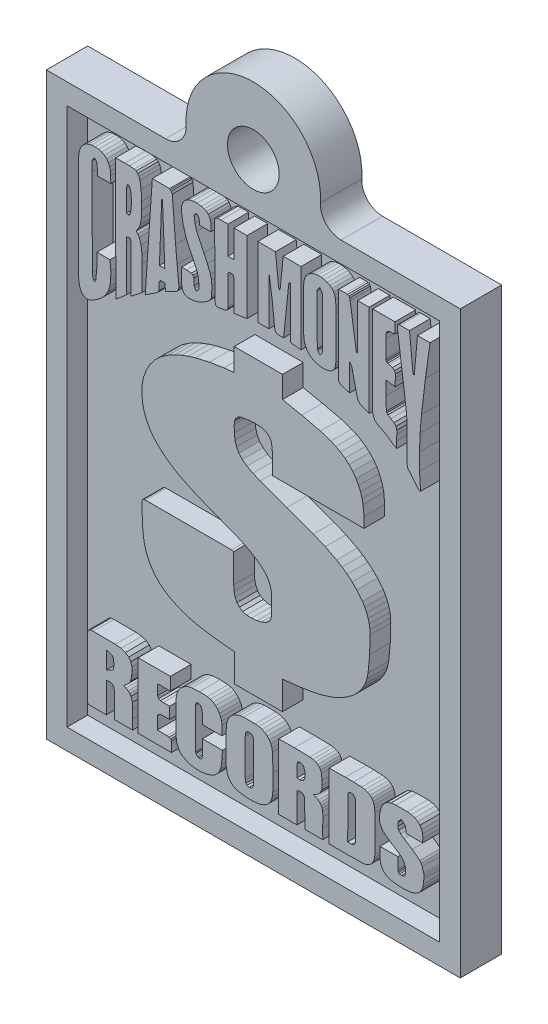
SolidWorks part; units mm, degrees
ref_plane "Front Plane" through (0, 0, 0) normal (0, 0, 1) x (1, 0, 0)
ref_plane "Top Plane" through (0, 0, 0) normal (0, 1, 0) x (1, 0, 0)
ref_plane "Right Plane" through (0, 0, 0) normal (1, 0, 0) x (0, 0, -1)
sketch "Sketch3" plane through (0, 0, 0) normal (0, 0, 1) x (1, 0, 0)
  line L1 (0, 0) -> (63.5, 0)
  line L2 (0, 0) -> (0, 88.9)
  line L3 (0, 88.9) -> (63.5, 88.9)
  line L4 (63.5, 0) -> (63.5, 88.9)
  dimension "D1" = 63.5
  dimension "D2" = 88.9
extrude "Boss-Extrude1" add sketch "Sketch3" along normal blind 6.35
sketch "Sketch4" plane through (0, 0, 6.35) normal (0, 0, 1) x (1, 0, 0)
  line L0 (3.175, 85.725) -> (3.175, 3.175)
  line L1 (3.175, 3.175) -> (60.325, 3.175)
  line L2 (60.325, 3.175) -> (60.325, 85.725)
  line L3 (60.325, 85.725) -> (3.175, 85.725)
  line L4 (0, 88.9) -> (0, 0)
  line L5 (0, 0) -> (63.5, 0)
  line L6 (63.5, 0) -> (63.5, 88.9)
  line L7 (63.5, 88.9) -> (0, 88.9)
  line L8 (0, 88.9) -> (0, 0) construction
  line L9 (0, 0) -> (63.5, 0) construction
  line L10 (63.5, 0) -> (63.5, 88.9) construction
  line L11 (63.5, 88.9) -> (0, 88.9) construction
  dimension "D1" = 0
  dimension "D2" = 3.175
extrude "Cut-Extrude1" cut sketch "Sketch4" against normal blind 3.175
sketch "Sketch5" plane through (0, 0, 3.175) normal (0, 0, 1) x (1, 0, 0)
  line L0 (36.2423, 26.0782) -> (36.2187, 21.7427)
  line L1 (38.9004, 26.3618) -> (36.2423, 26.0782)
  line L2 (40.6115, 26.6257) -> (38.9004, 26.3618)
  line L3 (42.2938, 26.9938) -> (40.6115, 26.6257)
  line L4 (43.9274, 27.5213) -> (42.2938, 26.9938)
  line L5 (44.7197, 27.8622) -> (43.9274, 27.5213)
  line L6 (45.4924, 28.2637) -> (44.7197, 27.8622)
  line L7 (46.2282, 28.7206) -> (45.4924, 28.2637)
  line L8 (46.9067, 29.2251) -> (46.2282, 28.7206)
  line L9 (47.5204, 29.7805) -> (46.9067, 29.2251)
  line L10 (48.0618, 30.3902) -> (47.5204, 29.7805)
  line L11 (48.5235, 31.0575) -> (48.0618, 30.3902)
  line L12 (48.898, 31.7857) -> (48.5235, 31.0575)
  line L13 (49.1778, 32.5781) -> (48.898, 31.7857)
  line L14 (49.3554, 33.4381) -> (49.1778, 32.5781)
  line L15 (49.5932, 36.04) -> (49.3554, 33.4381)
  line L16 (49.6626, 38.6597) -> (49.5932, 36.04)
  line L17 (49.6353, 39.3647) -> (49.6626, 38.6597)
  line L18 (49.5376, 40.0448) -> (49.6353, 39.3647)
  line L19 (49.3721, 40.7006) -> (49.5376, 40.0448)
  line L20 (49.1413, 41.3325) -> (49.3721, 40.7006)
  line L21 (48.848, 41.9412) -> (49.1413, 41.3325)
  line L22 (48.4947, 42.5272) -> (48.848, 41.9412)
  line L23 (47.6188, 43.6332) -> (48.4947, 42.5272)
  line L24 (46.9047, 44.3394) -> (47.6188, 43.6332)
  line L25 (46.1477, 44.9744) -> (46.9047, 44.3394)
  line L26 (45.3524, 45.5458) -> (46.1477, 44.9744)
  line L27 (44.5237, 46.0609) -> (45.3524, 45.5458)
  line L28 (42.7845, 46.9525) -> (44.5237, 46.0609)
  line L29 (40.9678, 47.7089) -> (42.7845, 46.9525)
  line L30 (36.8862, 49.193) -> (40.9678, 47.7089)
  line L31 (32.8046, 50.6859) -> (36.8862, 49.193)
  line L32 (31.6833, 51.1579) -> (32.8046, 50.6859)
  line L33 (30.7787, 51.6416) -> (31.6833, 51.1579)
  line L34 (30.0715, 52.161) -> (30.7787, 51.6416)
  line L35 (29.5425, 52.74) -> (30.0715, 52.161)
  line L36 (29.1725, 53.4027) -> (29.5425, 52.74)
  line L37 (28.9421, 54.173) -> (29.1725, 53.4027)
  line L38 (28.8321, 55.0748) -> (28.9421, 54.173)
  line L39 (28.8234, 56.2029) -> (28.8321, 55.0748)
  line L40 (28.8935, 56.7347) -> (28.8234, 56.2029)
  line L41 (29.101, 57.179) -> (28.8935, 56.7347)
  line L42 (29.4414, 57.5103) -> (29.101, 57.179)
  line L43 (29.9102, 57.7032) -> (29.4414, 57.5103)
  line L44 (31.2939, 57.9262) -> (29.9102, 57.7032)
  line L45 (31.9952, 57.964) -> (31.2939, 57.9262)
  line L46 (32.6864, 57.9277) -> (31.9952, 57.964)
  line L47 (33.1952, 57.8398) -> (32.6864, 57.9277)
  line L48 (33.6177, 57.6986) -> (33.1952, 57.8398)
  line L49 (33.9596, 57.5018) -> (33.6177, 57.6986)
  line L50 (34.2266, 57.2469) -> (33.9596, 57.5018)
  line L51 (34.4245, 56.9317) -> (34.2266, 57.2469)
  line L52 (34.5587, 56.5538) -> (34.4245, 56.9317)
  line L53 (34.6593, 55.6004) -> (34.5587, 56.5538)
  line L54 (34.6593, 52.3398) -> (34.6593, 55.6004)
  line L55 (48.7175, 52.3398) -> (34.6593, 52.3398)
  line L56 (48.7369, 53.9223) -> (48.7175, 52.3398)
  line L57 (48.589, 55.4572) -> (48.7369, 53.9223)
  line L58 (48.4306, 56.2043) -> (48.589, 55.4572)
  line L59 (48.2042, 56.9366) -> (48.4306, 56.2043)
  line L60 (47.9011, 57.6532) -> (48.2042, 56.9366)
  line L61 (47.5125, 58.353) -> (47.9011, 57.6532)
  line L62 (47.0008, 59.066) -> (47.5125, 58.353)
  line L63 (46.427, 59.6866) -> (47.0008, 59.066)
  line L64 (45.7974, 60.2234) -> (46.427, 59.6866)
  line L65 (45.1188, 60.6847) -> (45.7974, 60.2234)
  line L66 (44.3975, 61.079) -> (45.1188, 60.6847)
  line L67 (43.64, 61.4147) -> (44.3975, 61.079)
  line L68 (42.0428, 61.9443) -> (43.64, 61.4147)
  line L69 (39.1854, 62.6133) -> (42.0428, 61.9443)
  line L70 (36.2305, 63.2202) -> (39.1854, 62.6133)
  line L71 (36.2305, 66.5634) -> (36.2305, 63.2202)
  line L72 (28.8234, 66.5634) -> (36.2305, 66.5634)
  line L73 (28.8234, 63.102) -> (28.8234, 66.5634)
  line L74 (27.2286, 62.9248) -> (28.8234, 63.102)
  line L75 (25.0104, 62.569) -> (27.2286, 62.9248)
  line L76 (22.8354, 62.0713) -> (25.0104, 62.569)
  line L77 (21.7707, 61.7458) -> (22.8354, 62.0713)
  line L78 (20.7246, 61.3566) -> (21.7707, 61.7458)
  line L79 (19.6999, 60.8943) -> (20.7246, 61.3566)
  line L80 (18.6991, 60.3495) -> (19.6999, 60.8943)
  line L81 (17.6197, 59.6008) -> (18.6991, 60.3495)
  line L82 (16.6977, 58.7373) -> (17.6197, 59.6008)
  line L83 (15.9387, 57.7724) -> (16.6977, 58.7373)
  line L84 (15.3485, 56.7197) -> (15.9387, 57.7724)
  line L85 (14.9327, 55.5929) -> (15.3485, 56.7197)
  line L86 (14.6971, 54.4054) -> (14.9327, 55.5929)
  line L87 (14.6472, 53.1708) -> (14.6971, 54.4054)
  line L88 (14.7888, 51.9027) -> (14.6472, 53.1708)
  line L89 (15.0103, 50.9982) -> (14.7888, 51.9027)
  line L90 (15.3245, 50.1597) -> (15.0103, 50.9982)
  line L91 (15.7246, 49.3824) -> (15.3245, 50.1597)
  line L92 (16.2035, 48.6614) -> (15.7246, 49.3824)
  line L93 (16.7545, 47.9919) -> (16.2035, 48.6614)
  line L94 (17.3705, 47.3691) -> (16.7545, 47.9919)
  line L95 (18.0446, 46.7881) -> (17.3705, 47.3691)
  line L96 (18.77, 46.244) -> (18.0446, 46.7881)
  line L97 (19.6487, 45.6648) -> (18.77, 46.244)
  line L98 (20.5541, 45.1435) -> (19.6487, 45.6648)
  line L99 (22.4278, 44.2357) -> (20.5541, 45.1435)
  line L100 (24.357, 43.4431) -> (22.4278, 44.2357)
  line L101 (26.3071, 42.6881) -> (24.357, 43.4431)
  line L102 (29.4274, 41.4713) -> (26.3071, 42.6881)
  line L103 (30.9405, 40.7644) -> (29.4274, 41.4713)
  line L104 (32.3793, 39.9001) -> (30.9405, 40.7644)
  line L105 (33.3403, 39.0999) -> (32.3793, 39.9001)
  line L106 (33.7337, 38.6523) -> (33.3403, 39.0999)
  line L107 (34.0598, 38.1679) -> (33.7337, 38.6523)
  line L108 (34.3117, 37.6432) -> (34.0598, 38.1679)
  line L109 (34.4825, 37.0743) -> (34.3117, 37.6432)
  line L110 (34.5652, 36.4574) -> (34.4825, 37.0743)
  line L111 (34.553, 35.789) -> (34.5652, 36.4574)
  line L112 (34.5205, 34.7848) -> (34.553, 35.789)
  line L113 (34.5412, 33.7807) -> (34.5205, 34.7848)
  line L114 (34.4919, 33.2889) -> (34.5412, 33.7807)
  line L115 (34.3153, 32.8769) -> (34.4919, 33.2889)
  line L116 (34.0212, 32.5447) -> (34.3153, 32.8769)
  line L117 (33.6197, 32.2921) -> (34.0212, 32.5447)
  line L118 (32.9877, 32.047) -> (33.6197, 32.2921)
  line L119 (32.3202, 31.8905) -> (32.9877, 32.047)
  line L120 (31.4677, 31.7998) -> (32.3202, 31.8905)
  line L121 (30.7343, 31.8386) -> (31.4677, 31.7998)
  line L122 (30.1182, 32.0078) -> (30.7343, 31.8386)
  line L123 (29.6179, 32.3084) -> (30.1182, 32.0078)
  line L124 (29.2316, 32.7413) -> (29.6179, 32.3084)
  line L125 (28.9578, 33.3076) -> (29.2316, 32.7413)
  line L126 (28.7947, 34.0081) -> (28.9578, 33.3076)
  line L127 (28.7407, 34.8439) -> (28.7947, 34.0081)
  line L128 (28.7407, 39.2622) -> (28.7407, 34.8439)
  line L129 (28.4099, 39.3331) -> (28.7407, 39.2622)
  line L130 (15.2141, 39.3449) -> (28.4099, 39.3331)
  line L131 (14.9446, 39.3091) -> (15.2141, 39.3449)
  line L132 (14.7682, 39.2002) -> (14.9446, 39.3091)
  line L133 (14.6759, 39.0159) -> (14.7682, 39.2002)
  line L134 (14.6589, 38.7542) -> (14.6759, 39.0159)
  line L135 (14.7313, 36.4417) -> (14.6589, 38.7542)
  line L136 (14.7935, 35.2887) -> (14.7313, 36.4417)
  line L137 (14.9188, 34.1469) -> (14.7935, 35.2887)
  line L138 (15.1022, 33.2367) -> (14.9188, 34.1469)
  line L139 (15.3694, 32.377) -> (15.1022, 33.2367)
  line L140 (15.721, 31.5694) -> (15.3694, 32.377)
  line L141 (16.1577, 30.8154) -> (15.721, 31.5694)
  line L142 (16.6803, 30.1168) -> (16.1577, 30.8154)
  line L143 (17.2895, 29.4753) -> (16.6803, 30.1168)
  line L144 (17.9858, 28.8925) -> (17.2895, 29.4753)
  line L145 (18.77, 28.37) -> (17.9858, 28.8925)
  line L146 (20.2141, 27.6409) -> (18.77, 28.37)
  line L147 (21.719, 27.1089) -> (20.2141, 27.6409)
  line L148 (23.2704, 26.732) -> (21.719, 27.1089)
  line L149 (24.854, 26.468) -> (23.2704, 26.732)
  line L150 (26.8047, 26.2362) -> (24.854, 26.468)
  line L151 (28.8352, 26.0309) -> (26.8047, 26.2362)
  line L152 (28.8352, 21.7425) -> (28.8352, 26.0309)
  line L153 (36.2187, 21.7427) -> (28.8352, 21.7425)
  line L154 (9.8707, 79.8064) -> (9.8825, 78.7312)
  line L155 (9.8258, 80.3901) -> (9.8707, 79.8064)
  line L156 (9.7022, 80.9071) -> (9.8258, 80.3901)
  line L157 (9.5029, 81.3541) -> (9.7022, 80.9071)
  line L158 (9.2313, 81.7276) -> (9.5029, 81.3541)
  line L159 (8.8904, 82.0241) -> (9.2313, 81.7276)
  line L160 (8.4835, 82.2402) -> (8.8904, 82.0241)
  line L161 (8.0138, 82.3724) -> (8.4835, 82.2402)
  line L162 (7.4843, 82.4172) -> (8.0138, 82.3724)
  line L163 (6.9212, 82.3728) -> (7.4843, 82.4172)
  line L164 (6.4215, 82.2417) -> (6.9212, 82.3728)
  line L165 (5.9888, 82.0266) -> (6.4215, 82.2417)
  line L166 (5.6267, 81.7306) -> (5.9888, 82.0266)
  line L167 (5.3387, 81.3564) -> (5.6267, 81.7306)
  line L168 (5.1286, 80.9071) -> (5.3387, 81.3564)
  line L169 (4.9999, 80.3855) -> (5.1286, 80.9071)
  line L170 (4.9562, 79.7946) -> (4.9999, 80.3855)
  line L171 (4.9562, 63.8226) -> (4.9562, 79.7946)
  line L172 (5.002, 63.2098) -> (4.9562, 63.8226)
  line L173 (5.1453, 62.6058) -> (5.002, 63.2098)
  line L174 (5.2951, 62.242) -> (5.1453, 62.6058)
  line L175 (5.4777, 61.9568) -> (5.2951, 62.242)
  line L176 (5.6916, 61.7502) -> (5.4777, 61.9568)
  line L177 (5.9353, 61.6223) -> (5.6916, 61.7502)
  line L178 (6.2072, 61.573) -> (5.9353, 61.6223)
  line L179 (6.5058, 61.6024) -> (6.2072, 61.573)
  line L180 (7.1772, 61.897) -> (6.5058, 61.6024)
  line L181 (7.9231, 62.3994) -> (7.1772, 61.897)
  line L182 (8.5548, 62.9214) -> (7.9231, 62.3994)
  line L183 (9.0691, 63.5004) -> (8.5548, 62.9214)
  line L184 (9.4627, 64.1739) -> (9.0691, 63.5004)
  line L185 (9.7323, 64.9791) -> (9.4627, 64.1739)
  line L186 (9.8747, 65.9536) -> (9.7323, 64.9791)
  line L187 (9.8864, 67.1347) -> (9.8747, 65.9536)
  line L188 (9.7644, 68.5598) -> (9.8864, 67.1347)
  line L189 (7.756, 68.56) -> (9.7644, 68.5598)
  line L190 (7.7442, 66.5044) -> (7.756, 68.56)
  line L191 (7.567, 64.5552) -> (7.7442, 66.5044)
  line L192 (7.2362, 64.5549) -> (7.567, 64.5552)
  line L193 (7.1255, 65.0274) -> (7.2362, 64.5549)
  line L194 (7.059, 65.5) -> (7.1255, 65.0274)
  line L195 (7.0118, 78.8494) -> (7.059, 65.5)
  line L196 (7.0354, 80.3615) -> (7.0118, 78.8494)
  line L197 (7.1772, 80.6554) -> (7.0354, 80.3615)
  line L198 (7.3898, 80.9404) -> (7.1772, 80.6554)
  line L199 (7.635, 80.6436) -> (7.3898, 80.9404)
  line L200 (7.7915, 80.3379) -> (7.635, 80.6436)
  line L201 (7.8254, 79.5567) -> (7.7915, 80.3379)
  line L202 (7.8151, 78.7312) -> (7.8254, 79.5567)
  line L203 (9.8825, 78.7312) -> (7.8151, 78.7312)
  line L204 (12.308, 79.3039) -> (12.3009, 76.0217)
  line L205 (12.3569, 79.6891) -> (12.308, 79.3039)
  line L206 (12.4751, 79.894) -> (12.3569, 79.6891)
  line L207 (12.636, 79.9051) -> (12.4751, 79.894)
  line L208 (12.8129, 79.7091) -> (12.636, 79.9051)
  line L209 (12.9437, 79.2469) -> (12.8129, 79.7091)
  line L210 (13.0272, 78.4732) -> (12.9437, 79.2469)
  line L211 (13.048, 77.5779) -> (13.0272, 78.4732)
  line L212 (12.9907, 76.7511) -> (13.048, 77.5779)
  line L213 (12.8769, 76.2468) -> (12.9907, 76.7511)
  line L214 (12.7205, 75.9837) -> (12.8769, 76.2468)
  line L215 (12.5267, 75.922) -> (12.7205, 75.9837)
  line L216 (12.3009, 76.0217) -> (12.5267, 75.922)
  line L217 (10.6714, 63.7696) -> (10.5941, 82.5048)
  line L218 (12.2938, 65.1619) -> (10.6714, 63.7696)
  line L219 (12.2938, 72.2532) -> (12.2938, 65.1619)
  line L220 (12.2956, 72.7749) -> (12.2938, 72.2532)
  line L221 (12.3598, 72.9085) -> (12.2956, 72.7749)
  line L222 (12.5214, 72.9623) -> (12.3598, 72.9085)
  line L223 (12.7007, 72.9842) -> (12.5214, 72.9623)
  line L224 (12.8467, 72.9547) -> (12.7007, 72.9842)
  line L225 (12.9474, 72.7771) -> (12.8467, 72.9547)
  line L226 (12.9907, 72.3545) -> (12.9474, 72.7771)
  line L227 (13.0121, 68.8089) -> (12.9907, 72.3545)
  line L228 (13.0121, 65.3366) -> (13.0121, 68.8089)
  line L229 (14.6762, 66.6515) -> (13.0121, 65.3366)
  line L230 (14.6833, 70.4904) -> (14.6762, 66.6515)
  line L231 (14.6652, 71.8079) -> (14.6833, 70.4904)
  line L232 (14.5278, 72.9166) -> (14.6652, 71.8079)
  line L233 (14.2423, 73.7897) -> (14.5278, 72.9166)
  line L234 (14.0351, 74.1296) -> (14.2423, 73.7897)
  line L235 (13.7801, 74.4007) -> (14.0351, 74.1296)
  line L236 (14.1561, 74.935) -> (13.7801, 74.4007)
  line L237 (14.4246, 75.6213) -> (14.1561, 74.935)
  line L238 (14.5772, 76.4976) -> (14.4246, 75.6213)
  line L239 (14.6051, 77.6018) -> (14.5772, 76.4976)
  line L240 (14.6051, 78.7769) -> (14.6051, 77.6018)
  line L241 (14.5456, 80.3132) -> (14.6051, 78.7769)
  line L242 (14.3526, 81.4336) -> (14.5456, 80.3132)
  line L243 (14.1995, 81.8407) -> (14.3526, 81.4336)
  line L244 (14.0051, 82.1474) -> (14.1995, 81.8407)
  line L245 (13.7666, 82.3549) -> (14.0051, 82.1474)
  line L246 (13.4814, 82.4643) -> (13.7666, 82.3549)
  line L247 (12.7693, 82.5476) -> (13.4814, 82.4643)
  line L248 (12.0511, 82.553) -> (12.7693, 82.5476)
  line L249 (10.5941, 82.5048) -> (12.0511, 82.553)
  line L250 (18.1707, 71.5746) -> (17.8162, 80.5649)
  line L251 (17.3437, 71.5745) -> (18.1707, 71.5746)
  line L252 (17.6981, 80.5647) -> (17.3437, 71.5745)
  line L253 (17.8162, 80.5649) -> (17.6981, 80.5647)
  line L254 (18.9134, 68.9312) -> (18.2887, 68.5738)
  line L255 (19.9352, 69.4056) -> (18.9134, 68.9312)
  line L256 (20.1996, 69.702) -> (19.9352, 69.4056)
  line L257 (20.3177, 70.0871) -> (20.1996, 69.702)
  line L258 (20.3207, 70.5585) -> (20.3177, 70.0871)
  line L259 (20.0593, 73.1043) -> (20.3207, 70.5585)
  line L260 (19.8245, 75.6502) -> (20.0593, 73.1043)
  line L261 (19.3165, 82.0413) -> (19.8245, 75.6502)
  line L262 (19.1615, 82.3736) -> (19.3165, 82.0413)
  line L263 (19.0258, 82.5115) -> (19.1615, 82.3736)
  line L264 (18.8912, 82.5729) -> (19.0258, 82.5115)
  line L265 (16.2568, 82.5966) -> (18.8912, 82.5729)
  line L266 (15.1699, 66.6009) -> (16.2568, 82.5966)
  line L267 (16.942, 67.7705) -> (15.1699, 66.6009)
  line L268 (17.1571, 67.967) -> (16.942, 67.7705)
  line L269 (17.272, 68.1889) -> (17.1571, 67.967)
  line L270 (17.3141, 68.6816) -> (17.272, 68.1889)
  line L271 (17.2942, 69.1942) -> (17.3141, 68.6816)
  line L272 (17.3315, 69.441) -> (17.2942, 69.1942)
  line L273 (17.4381, 69.6725) -> (17.3315, 69.441)
  line L274 (18.1824, 69.6727) -> (17.4381, 69.6725)
  line L275 (18.2887, 68.5738) -> (18.1824, 69.6727)
  line L276 (25.2608, 81.0911) -> (25.2236, 80.0096)
  line L277 (25.1891, 81.5141) -> (25.2608, 81.0911)
  line L278 (25.0523, 81.8658) -> (25.1891, 81.5141)
  line L279 (24.8468, 82.1517) -> (25.0523, 81.8658)
  line L280 (24.569, 82.377) -> (24.8468, 82.1517)
  line L281 (24.2154, 82.5472) -> (24.569, 82.377)
  line L282 (23.7823, 82.6677) -> (24.2154, 82.5472)
  line L283 (23.1096, 82.7562) -> (23.7823, 82.6677)
  line L284 (22.492, 82.7312) -> (23.1096, 82.7562)
  line L285 (21.9437, 82.5954) -> (22.492, 82.7312)
  line L286 (21.4786, 82.3517) -> (21.9437, 82.5954)
  line L287 (21.1111, 82.0027) -> (21.4786, 82.3517)
  line L288 (20.8551, 81.5513) -> (21.1111, 82.0027)
  line L289 (20.7248, 81.0002) -> (20.8551, 81.5513)
  line L290 (20.7344, 80.3522) -> (20.7248, 81.0002)
  line L291 (21.0002, 78.8061) -> (20.7344, 80.3522)
  line L292 (21.4432, 77.3043) -> (21.0002, 78.8061)
  line L293 (21.8384, 76.3888) -> (21.4432, 77.3043)
  line L294 (22.2834, 75.4909) -> (21.8384, 76.3888)
  line L295 (22.7307, 74.5931) -> (22.2834, 75.4909)
  line L296 (23.1325, 73.6775) -> (22.7307, 74.5931)
  line L297 (23.2833, 73.1688) -> (23.1325, 73.6775)
  line L298 (23.3644, 72.6291) -> (23.2833, 73.1688)
  line L299 (23.4279, 71.5275) -> (23.3644, 72.6291)
  line L300 (23.3862, 71.3995) -> (23.4279, 71.5275)
  line L301 (23.2713, 71.2661) -> (23.3862, 71.3995)
  line L302 (22.9908, 70.9958) -> (23.2713, 71.2661)
  line L303 (22.8047, 71.2749) -> (22.9908, 70.9958)
  line L304 (22.6718, 71.5629) -> (22.8047, 71.2749)
  line L305 (22.6364, 72.5907) -> (22.6718, 71.5629)
  line L306 (22.4872, 72.8772) -> (22.6364, 72.5907)
  line L307 (22.2583, 73.0396) -> (22.4872, 72.8772)
  line L308 (21.5141, 73.0736) -> (22.2583, 73.0396)
  line L309 (20.7344, 73.0632) -> (21.5141, 73.0736)
  line L310 (20.7226, 71.8715) -> (20.7344, 73.0632)
  line L311 (20.7462, 70.7596) -> (20.7226, 71.8715)
  line L312 (20.8387, 70.2464) -> (20.7462, 70.7596)
  line L313 (21.0519, 69.8529) -> (20.8387, 70.2464)
  line L314 (21.3692, 69.5967) -> (21.0519, 69.8529)
  line L315 (21.774, 69.4955) -> (21.3692, 69.5967)
  line L316 (22.6421, 69.552) -> (21.774, 69.4955)
  line L317 (23.4559, 69.779) -> (22.6421, 69.552)
  line L318 (24.2144, 70.1567) -> (23.4559, 69.779)
  line L319 (24.9164, 70.6651) -> (24.2144, 70.1567)
  line L320 (25.225, 71.0431) -> (24.9164, 70.6651)
  line L321 (25.3267, 71.2698) -> (25.225, 71.0431)
  line L322 (25.3653, 71.492) -> (25.3267, 71.2698)
  line L323 (25.386, 72.9569) -> (25.3653, 71.492)
  line L324 (25.3354, 73.6749) -> (25.386, 72.9569)
  line L325 (25.1763, 74.3509) -> (25.3354, 73.6749)
  line L326 (24.7014, 75.528) -> (25.1763, 74.3509)
  line L327 (24.1589, 76.6797) -> (24.7014, 75.528)
  line L328 (23.0617, 78.9818) -> (24.1589, 76.6797)
  line L329 (22.8047, 79.9225) -> (23.0617, 78.9818)
  line L330 (22.6718, 80.9075) -> (22.8047, 79.9225)
  line L331 (22.7914, 81.129) -> (22.6718, 80.9075)
  line L332 (23.0262, 81.3682) -> (22.7914, 81.129)
  line L333 (23.2684, 81.1467) -> (23.0262, 81.3682)
  line L334 (23.4397, 80.9075) -> (23.2684, 81.1467)
  line L335 (23.4973, 80.4763) -> (23.4397, 80.9075)
  line L336 (23.5106, 80.0096) -> (23.4973, 80.4763)
  line L337 (25.2236, 80.0096) -> (23.5106, 80.0096)
  line L338 (27.8686, 78.0828) -> (28.7782, 78.0828)
  line L339 (27.8686, 82.3357) -> (27.8686, 78.0828)
  line L340 (26.7817, 82.3357) -> (27.8686, 82.3357)
  line L341 (26.22, 82.321) -> (26.7817, 82.3357)
  line L342 (25.9297, 82.2176) -> (26.22, 82.321)
  line L343 (25.8232, 81.937) -> (25.9297, 82.2176)
  line L344 (25.813, 81.3907) -> (25.8232, 81.937)
  line L345 (25.8839, 71.8571) -> (25.813, 81.3907)
  line L346 (25.9009, 70.998) -> (25.8839, 71.8571)
  line L347 (25.9487, 70.7461) -> (25.9009, 70.998)
  line L348 (26.0463, 70.593) -> (25.9487, 70.7461)
  line L349 (26.2115, 70.5241) -> (26.0463, 70.593)
  line L350 (26.462, 70.5247) -> (26.2115, 70.5241)
  line L351 (27.2897, 70.6757) -> (26.462, 70.5247)
  line L352 (27.5681, 70.7634) -> (27.2897, 70.6757)
  line L353 (27.7534, 70.8987) -> (27.5681, 70.7634)
  line L354 (27.8546, 71.1027) -> (27.7534, 70.8987)
  line L355 (27.8804, 71.3963) -> (27.8546, 71.1027)
  line L356 (27.8686, 75.4012) -> (27.8804, 71.3963)
  line L357 (27.8878, 75.8442) -> (27.8686, 75.4012)
  line L358 (28.0131, 76.0059) -> (27.8878, 75.8442)
  line L359 (28.3057, 76.0745) -> (28.0131, 76.0059)
  line L360 (28.597, 76.0229) -> (28.3057, 76.0745)
  line L361 (28.731, 75.8737) -> (28.597, 76.0229)
  line L362 (28.7664, 75.4248) -> (28.731, 75.8737)
  line L363 (28.7664, 70.9474) -> (28.7664, 75.4248)
  line L364 (30.7866, 71.2546) -> (28.7664, 70.9474)
  line L365 (30.7866, 82.2885) -> (30.7866, 71.2546)
  line L366 (28.7782, 82.2885) -> (30.7866, 82.2885)
  line L367 (28.7782, 78.0828) -> (28.7782, 82.2885)
  line L368 (39.066, 82.3121) -> (39.066, 71.2309)
  line L369 (36.3371, 82.3121) -> (39.066, 82.3121)
  line L370 (35.8527, 77.5748) -> (36.3371, 82.3121)
  line L371 (35.6637, 77.5748) -> (35.8527, 77.5748)
  line L372 (35.1557, 82.3239) -> (35.6637, 77.5748)
  line L373 (32.4386, 82.3239) -> (35.1557, 82.3239)
  line L374 (32.4386, 71.5735) -> (32.4386, 82.3239)
  line L375 (34.1397, 71.5735) -> (32.4386, 71.5735)
  line L376 (34.1397, 79.146) -> (34.1397, 71.5735)
  line L377 (34.6477, 75.6891) -> (34.1397, 79.146)
  line L378 (35.0139, 72.2233) -> (34.6477, 75.6891)
  line L379 (35.0719, 71.8829) -> (35.0139, 72.2233)
  line L380 (35.1941, 71.6444) -> (35.0719, 71.8829)
  line L381 (35.4093, 71.5122) -> (35.1941, 71.6444)
  line L382 (35.7464, 71.4908) -> (35.4093, 71.5122)
  line L383 (36.3961, 71.4908) -> (35.7464, 71.4908)
  line L384 (37.2113, 79.276) -> (36.3961, 71.4908)
  line L385 (37.4239, 79.2642) -> (37.2113, 79.276)
  line L386 (37.4239, 71.4081) -> (37.4239, 79.2642)
  line L387 (39.066, 71.2309) -> (37.4239, 71.4081)
  line L388 (42.3882, 74.5197) -> (42.3838, 76.3804)
  line L389 (42.3483, 72.6591) -> (42.3882, 74.5197)
  line L390 (42.2199, 72.3106) -> (42.3483, 72.6591)
  line L391 (42.0184, 71.9999) -> (42.2199, 72.3106)
  line L392 (41.7444, 72.3002) -> (42.0184, 71.9999)
  line L393 (41.6194, 72.4721) -> (41.7444, 72.3002)
  line L394 (41.5686, 72.6472) -> (41.6194, 72.4721)
  line L395 (41.4977, 80.2316) -> (41.5686, 72.6472)
  line L396 (41.5443, 80.4158) -> (41.4977, 80.2316)
  line L397 (41.6572, 80.5978) -> (41.5443, 80.4158)
  line L398 (41.923, 80.9641) -> (41.6572, 80.5978)
  line L399 (42.1947, 80.6082) -> (41.923, 80.9641)
  line L400 (42.3085, 80.4275) -> (42.1947, 80.6082)
  line L401 (42.3601, 80.2434) -> (42.3085, 80.4275)
  line L402 (42.3838, 76.3804) -> (42.3601, 80.2434)
  line L403 (44.4039, 78.7903) -> (44.4039, 72.222)
  line L404 (44.4128, 79.728) -> (44.4039, 78.7903)
  line L405 (44.3685, 80.6569) -> (44.4128, 79.728)
  line L406 (44.2676, 81.08) -> (44.3685, 80.6569)
  line L407 (44.0844, 81.4523) -> (44.2676, 81.08)
  line L408 (43.825, 81.7706) -> (44.0844, 81.4523)
  line L409 (43.4957, 82.0317) -> (43.825, 81.7706)
  line L410 (43.1028, 82.2324) -> (43.4957, 82.0317)
  line L411 (42.6523, 82.3697) -> (43.1028, 82.2324)
  line L412 (42.1507, 82.4402) -> (42.6523, 82.3697)
  line L413 (41.6041, 82.4407) -> (42.1507, 82.4402)
  line L414 (41.157, 82.3723) -> (41.6041, 82.4407)
  line L415 (40.7502, 82.2323) -> (41.157, 82.3723)
  line L416 (40.3893, 82.0256) -> (40.7502, 82.2323)
  line L417 (40.0801, 81.757) -> (40.3893, 82.0256)
  line L418 (39.8286, 81.4314) -> (40.0801, 81.757)
  line L419 (39.6404, 81.0536) -> (39.8286, 81.4314)
  line L420 (39.5215, 80.6284) -> (39.6404, 81.0536)
  line L421 (39.4776, 80.1607) -> (39.5215, 80.6284)
  line L422 (39.4776, 73.5924) -> (39.4776, 80.1607)
  line L423 (39.5328, 72.8842) -> (39.4776, 73.5924)
  line L424 (39.6956, 72.2596) -> (39.5328, 72.8842)
  line L425 (39.9617, 71.7226) -> (39.6956, 72.2596)
  line L426 (40.3267, 71.2769) -> (39.9617, 71.7226)
  line L427 (40.7865, 70.9265) -> (40.3267, 71.2769)
  line L428 (41.3366, 70.6751) -> (40.7865, 70.9265)
  line L429 (41.9729, 70.5268) -> (41.3366, 70.6751)
  line L430 (42.6909, 70.4854) -> (41.9729, 70.5268)
  line L431 (43.4071, 70.6155) -> (42.6909, 70.4854)
  line L432 (43.7002, 70.7618) -> (43.4071, 70.6155)
  line L433 (43.9461, 70.9594) -> (43.7002, 70.7618)
  line L434 (44.1422, 71.2063) -> (43.9461, 70.9594)
  line L435 (44.2858, 71.5004) -> (44.1422, 71.2063)
  line L436 (44.3739, 71.8397) -> (44.2858, 71.5004)
  line L437 (44.4039, 72.222) -> (44.3739, 71.8397)
  line L438 (49.5284, 82.1339) -> (49.5166, 68.0048)
  line L439 (47.7564, 82.1339) -> (49.5284, 82.1339)
  line L440 (47.7564, 75.0693) -> (47.7564, 82.1339)
  line L441 (47.588, 75.183) -> (47.7564, 75.0693)
  line L442 (47.5437, 75.3056) -> (47.588, 75.183)
  line L443 (46.5986, 81.5668) -> (47.5437, 75.3056)
  line L444 (46.5314, 81.8624) -> (46.5986, 81.5668)
  line L445 (46.4067, 82.0615) -> (46.5314, 81.8624)
  line L446 (46.2066, 82.1699) -> (46.4067, 82.0615)
  line L447 (45.9134, 82.193) -> (46.2066, 82.1699)
  line L448 (44.8738, 82.193) -> (45.9134, 82.193)
  line L449 (44.7911, 81.9685) -> (44.8738, 82.193)
  line L450 (44.7911, 70.2258) -> (44.7911, 81.9685)
  line L451 (44.893, 69.926) -> (44.7911, 70.2258)
  line L452 (45.1101, 69.706) -> (44.893, 69.926)
  line L453 (45.7569, 69.4712) -> (45.1101, 69.706)
  line L454 (46.5277, 69.2452) -> (45.7569, 69.4712)
  line L455 (46.5277, 73.3682) -> (46.5277, 69.2452)
  line L456 (46.7714, 73.0994) -> (46.5277, 73.3682)
  line L457 (46.8822, 72.8129) -> (46.7714, 73.0994)
  line L458 (47.6973, 69.257) -> (46.8822, 72.8129)
  line L459 (47.845, 68.8879) -> (47.6973, 69.257)
  line L460 (48.099, 68.6073) -> (47.845, 68.8879)
  line L461 (48.7546, 68.2972) -> (48.099, 68.6073)
  line L462 (49.5166, 68.0048) -> (48.7546, 68.2972)
  line L463 (50.0536, 81.2831) -> (50.0654, 82.1691)
  line L464 (50.0639, 75.2404) -> (50.0536, 81.2831)
  line L465 (50.0299, 69.1978) -> (50.0639, 75.2404)
  line L466 (50.0613, 68.4552) -> (50.0299, 69.1978)
  line L467 (50.2367, 67.8378) -> (50.0613, 68.4552)
  line L468 (50.3998, 67.5749) -> (50.2367, 67.8378)
  line L469 (50.6247, 67.3421) -> (50.3998, 67.5749)
  line L470 (50.9199, 67.139) -> (50.6247, 67.3421)
  line L471 (51.294, 66.965) -> (50.9199, 67.139)
  line L472 (51.7992, 66.7252) -> (51.294, 66.965)
  line L473 (52.2789, 66.4201) -> (51.7992, 66.7252)
  line L474 (53.2196, 65.76) -> (52.2789, 66.4201)
  line L475 (53.7512, 65.4647) -> (53.2196, 65.76)
  line L476 (53.735, 66.4541) -> (53.7512, 65.4647)
  line L477 (53.763, 67.3549) -> (53.735, 66.4541)
  line L478 (53.7621, 67.8987) -> (53.763, 67.3549)
  line L479 (53.6227, 68.3472) -> (53.7621, 67.8987)
  line L480 (53.3261, 68.7072) -> (53.6227, 68.3472)
  line L481 (52.8534, 68.9851) -> (53.3261, 68.7072)
  line L482 (52.403, 69.2657) -> (52.8534, 68.9851)
  line L483 (52.2304, 69.4503) -> (52.403, 69.2657)
  line L484 (52.1564, 69.6349) -> (52.2304, 69.4503)
  line L485 (52.1121, 71.6639) -> (52.1564, 69.6349)
  line L486 (52.1209, 73.746) -> (52.1121, 71.6639)
  line L487 (53.5268, 73.557) -> (52.1209, 73.746)
  line L488 (53.5149, 74.1728) -> (53.5268, 73.557)
  line L489 (53.5386, 74.7266) -> (53.5149, 74.1728)
  line L490 (53.5552, 75.2504) -> (53.5386, 74.7266)
  line L491 (53.4145, 75.648) -> (53.5552, 75.2504)
  line L492 (53.0967, 75.9127) -> (53.4145, 75.648)
  line L493 (52.5817, 76.0379) -> (53.0967, 75.9127)
  line L494 (52.3467, 76.099) -> (52.5817, 76.0379)
  line L495 (52.1992, 76.2254) -> (52.3467, 76.099)
  line L496 (52.1248, 76.4117) -> (52.1992, 76.2254)
  line L497 (52.1091, 76.6522) -> (52.1248, 76.4117)
  line L498 (52.1209, 79.2748) -> (52.1091, 76.6522)
  line L499 (52.1385, 79.9452) -> (52.1209, 79.2748)
  line L500 (52.2612, 80.2967) -> (52.1385, 79.9452)
  line L501 (52.5944, 80.4443) -> (52.2612, 80.2967)
  line L502 (53.2432, 80.5034) -> (52.5944, 80.4443)
  line L503 (53.4795, 80.5743) -> (53.2432, 80.5034)
  line L504 (53.4795, 82.1691) -> (53.4795, 80.5743)
  line L505 (50.0654, 82.1691) -> (53.4795, 82.1691)
  line L506 (54.3055, 82.1273) -> (55.7113, 82.1155)
  line L507 (54.0525, 82.0987) -> (54.3055, 82.1273)
  line L508 (53.9024, 81.9959) -> (54.0525, 82.0987)
  line L509 (53.8387, 81.82) -> (53.9024, 81.9959)
  line L510 (53.8448, 81.5721) -> (53.8387, 81.82)
  line L511 (54.8726, 73.9877) -> (53.8448, 81.5721)
  line L512 (55.2609, 70.7759) -> (54.8726, 73.9877)
  line L513 (55.3627, 69.1617) -> (55.2609, 70.7759)
  line L514 (55.3569, 67.5375) -> (55.3627, 69.1617)
  line L515 (55.3348, 65.9131) -> (55.3569, 67.5375)
  line L516 (55.3569, 64.2888) -> (55.3348, 65.9131)
  line L517 (55.3776, 63.9373) -> (55.3569, 64.2888)
  line L518 (55.4869, 63.639) -> (55.3776, 63.9373)
  line L519 (57.188, 61.6189) -> (55.4869, 63.639)
  line L520 (57.4125, 61.6189) -> (57.188, 61.6189)
  line L521 (57.2535, 64.1959) -> (57.4125, 61.6189)
  line L522 (57.2392, 66.763) -> (57.2535, 64.1959)
  line L523 (57.3458, 69.3223) -> (57.2392, 66.763)
  line L524 (57.5498, 71.8761) -> (57.3458, 69.3223)
  line L525 (58.1551, 76.9759) -> (57.5498, 71.8761)
  line L526 (58.8656, 82.0801) -> (58.1551, 76.9759)
  line L527 (56.94, 82.0801) -> (58.8656, 82.0801)
  line L528 (56.4438, 76.5868) -> (56.94, 82.0801)
  line L529 (56.2548, 76.5986) -> (56.4438, 76.5868)
  line L530 (55.7113, 82.1155) -> (56.2548, 76.5986)
  line L531 (51.1983, 9.8344) -> (51.1746, 11.3347)
  line L532 (51.2289, 9.4159) -> (51.1983, 9.8344)
  line L533 (51.3193, 9.0311) -> (51.2289, 9.4159)
  line L534 (51.4674, 8.684) -> (51.3193, 9.0311)
  line L535 (51.6708, 8.3784) -> (51.4674, 8.684)
  line L536 (51.9274, 8.1182) -> (51.6708, 8.3784)
  line L537 (52.2349, 7.9073) -> (51.9274, 8.1182)
  line L538 (52.5912, 7.7496) -> (52.2349, 7.9073)
  line L539 (52.9939, 7.6489) -> (52.5912, 7.7496)
  line L540 (54.1177, 7.5219) -> (52.9939, 7.6489)
  line L541 (55.2503, 7.5189) -> (54.1177, 7.5219)
  line L542 (55.9038, 7.5986) -> (55.2503, 7.5189)
  line L543 (56.4581, 7.7512) -> (55.9038, 7.5986)
  line L544 (56.9168, 7.9795) -> (56.4581, 7.7512)
  line L545 (57.2837, 8.2868) -> (56.9168, 7.9795)
  line L546 (57.5626, 8.6761) -> (57.2837, 8.2868)
  line L547 (57.7572, 9.1503) -> (57.5626, 8.6761)
  line L548 (57.8712, 9.7126) -> (57.7572, 9.1503)
  line L549 (57.9084, 10.366) -> (57.8712, 9.7126)
  line L550 (57.9291, 10.7529) -> (57.9084, 10.366)
  line L551 (57.8966, 11.1221) -> (57.9291, 10.7529)
  line L552 (57.6662, 11.8959) -> (57.8966, 11.1221)
  line L553 (57.5112, 12.2484) -> (57.6662, 11.8959)
  line L554 (57.2941, 12.5279) -> (57.5112, 12.2484)
  line L555 (56.1231, 13.4198) -> (57.2941, 12.5279)
  line L556 (54.8723, 14.2054) -> (56.1231, 13.4198)
  line L557 (54.3595, 14.5613) -> (54.8723, 14.2054)
  line L558 (54.0483, 14.9172) -> (54.3595, 14.5613)
  line L559 (53.9187, 15.3484) -> (54.0483, 14.9172)
  line L560 (53.9508, 15.9302) -> (53.9187, 15.3484)
  line L561 (54.02, 16.0927) -> (53.9508, 15.9302)
  line L562 (54.1502, 16.2462) -> (54.02, 16.0927)
  line L563 (54.447, 16.5445) -> (54.1502, 16.2462)
  line L564 (54.7999, 16.2728) -> (54.447, 16.5445)
  line L565 (55.0731, 15.9657) -> (54.7999, 16.2728)
  line L566 (55.1602, 15.5286) -> (55.0731, 15.9657)
  line L567 (55.1676, 15.056) -> (55.1602, 15.5286)
  line L568 (57.6957, 15.056) -> (55.1676, 15.056)
  line L569 (57.7634, 15.7043) -> (57.6957, 15.056)
  line L570 (57.7208, 16.282) -> (57.7634, 15.7043)
  line L571 (57.572, 16.785) -> (57.7208, 16.282)
  line L572 (57.3207, 17.209) -> (57.572, 16.785)
  line L573 (56.9708, 17.55) -> (57.3207, 17.209)
  line L574 (56.5262, 17.8038) -> (56.9708, 17.55)
  line L575 (55.9908, 17.9662) -> (56.5262, 17.8038)
  line L576 (55.3685, 18.033) -> (55.9908, 17.9662)
  line L577 (53.6437, 18.033) -> (55.3685, 18.033)
  line L578 (52.8787, 17.947) -> (53.6437, 18.033)
  line L579 (52.2201, 17.6727) -> (52.8787, 17.947)
  line L580 (51.7033, 17.2124) -> (52.2201, 17.6727)
  line L581 (51.5091, 16.9131) -> (51.7033, 17.2124)
  line L582 (51.3637, 16.5682) -> (51.5091, 16.9131)
  line L583 (51.1527, 15.7722) -> (51.3637, 16.5682)
  line L584 (51.0934, 14.9586) -> (51.1527, 15.7722)
  line L585 (51.1487, 14.5603) -> (51.0934, 14.9586)
  line L586 (51.2756, 14.1759) -> (51.1487, 14.5603)
  line L587 (51.4853, 13.8114) -> (51.2756, 14.1759)
  line L588 (51.7889, 13.473) -> (51.4853, 13.8114)
  line L589 (52.8138, 12.6815) -> (51.7889, 13.473)
  line L590 (53.9272, 11.9963) -> (52.8138, 12.6815)
  line L591 (54.5088, 11.5671) -> (53.9272, 11.9963)
  line L592 (54.9122, 11.0615) -> (54.5088, 11.5671)
  line L593 (55.1183, 10.4563) -> (54.9122, 11.0615)
  line L594 (55.1086, 9.7281) -> (55.1183, 10.4563)
  line L595 (55.0436, 9.4573) -> (55.1086, 9.7281)
  line L596 (54.9255, 9.2541) -> (55.0436, 9.4573)
  line L597 (54.7364, 9.1284) -> (54.9255, 9.2541)
  line L598 (54.4588, 9.0901) -> (54.7364, 9.1284)
  line L599 (54.1882, 9.1418) -> (54.4588, 9.0901)
  line L600 (54.0306, 9.2821) -> (54.1882, 9.1418)
  line L601 (53.9571, 9.4889) -> (54.0306, 9.2821)
  line L602 (53.939, 9.7399) -> (53.9571, 9.4889)
  line L603 (53.939, 11.3347) -> (53.939, 9.7399)
  line L604 (51.1746, 11.3347) -> (53.939, 11.3347)
  line L605 (46.2482, 15.8829) -> (46.2364, 9.4445)
  line L606 (46.4328, 16.1192) -> (46.2482, 15.8829)
  line L607 (46.7326, 16.2492) -> (46.4328, 16.1192)
  line L608 (47.0862, 16.1491) -> (46.7326, 16.2492)
  line L609 (47.3114, 15.9361) -> (47.0862, 16.1491)
  line L610 (47.4303, 15.6345) -> (47.3114, 15.9361)
  line L611 (47.465, 15.2686) -> (47.4303, 15.6345)
  line L612 (47.465, 10.366) -> (47.465, 15.2686)
  line L613 (47.401, 9.8682) -> (47.465, 10.366)
  line L614 (47.2007, 9.5641) -> (47.401, 9.8682)
  line L615 (46.8254, 9.4307) -> (47.2007, 9.5641)
  line L616 (46.2364, 9.4445) -> (46.8254, 9.4307)
  line L617 (43.3775, 7.7552) -> (43.3775, 17.8322)
  line L618 (45.9809, 7.7404) -> (43.3775, 7.7552)
  line L619 (48.5401, 7.7788) -> (45.9809, 7.7404)
  line L620 (48.9522, 7.8332) -> (48.5401, 7.7788)
  line L621 (49.3183, 7.9572) -> (48.9522, 7.8332)
  line L622 (49.6357, 8.1447) -> (49.3183, 7.9572)
  line L623 (49.9016, 8.3902) -> (49.6357, 8.1447)
  line L624 (50.1132, 8.6877) -> (49.9016, 8.3902)
  line L625 (50.2678, 9.0314) -> (50.1132, 8.6877)
  line L626 (50.3626, 9.4156) -> (50.2678, 9.0314)
  line L627 (50.3948, 9.8344) -> (50.3626, 9.4156)
  line L628 (50.3948, 15.434) -> (50.3948, 9.8344)
  line L629 (50.3676, 15.9513) -> (50.3948, 15.434)
  line L630 (50.2833, 16.4046) -> (50.3676, 15.9513)
  line L631 (50.1381, 16.7942) -> (50.2833, 16.4046)
  line L632 (49.9282, 17.1204) -> (50.1381, 16.7942)
  line L633 (49.6495, 17.3835) -> (49.9282, 17.1204)
  line L634 (49.2984, 17.5838) -> (49.6495, 17.3835)
  line L635 (48.8708, 17.7214) -> (49.2984, 17.5838)
  line L636 (48.3629, 17.7968) -> (48.8708, 17.7214)
  line L637 (47.127, 17.8571) -> (48.3629, 17.7968)
  line L638 (45.8835, 17.8632) -> (47.127, 17.8571)
  line L639 (43.3775, 17.8322) -> (45.8835, 17.8632)
  line L640 (38.4752, 15.9775) -> (38.4634, 14.0637)
  line L641 (38.5564, 16.2021) -> (38.4752, 15.9775)
  line L642 (38.7528, 16.3215) -> (38.5564, 16.2021)
  line L643 (39.0201, 16.328) -> (38.7528, 16.3215)
  line L644 (39.3139, 16.2137) -> (39.0201, 16.328)
  line L645 (39.5312, 15.9442) -> (39.3139, 16.2137)
  line L646 (39.6698, 15.4931) -> (39.5312, 15.9442)
  line L647 (39.7043, 14.9711) -> (39.6698, 15.4931)
  line L648 (39.6093, 14.489) -> (39.7043, 14.9711)
  line L649 (39.4203, 14.1949) -> (39.6093, 14.489)
  line L650 (39.1604, 14.0415) -> (39.4203, 14.1949)
  line L651 (38.8384, 14.0055) -> (39.1604, 14.0415)
  line L652 (38.4634, 14.0637) -> (38.8384, 14.0055)
  line L653 (35.6281, 7.8143) -> (35.6281, 17.844)
  line L654 (38.4515, 7.8143) -> (35.6281, 7.8143)
  line L655 (38.4515, 11.8663) -> (38.4515, 7.8143)
  line L656 (38.4545, 12.2887) -> (38.4515, 11.8663)
  line L657 (38.5612, 12.4478) -> (38.4545, 12.2887)
  line L658 (38.8296, 12.5161) -> (38.5612, 12.4478)
  line L659 (39.1275, 12.4919) -> (38.8296, 12.5161)
  line L660 (39.3701, 12.3935) -> (39.1275, 12.4919)
  line L661 (39.5373, 12.2087) -> (39.3701, 12.3935)
  line L662 (39.6093, 11.9254) -> (39.5373, 12.2087)
  line L663 (39.6447, 9.858) -> (39.6093, 11.9254)
  line L664 (39.6447, 7.8261) -> (39.6447, 9.858)
  line L665 (42.4091, 7.8261) -> (39.6447, 7.8261)
  line L666 (42.3929, 9.3545) -> (42.4091, 7.8261)
  line L667 (42.4209, 10.8385) -> (42.3929, 9.3545)
  line L668 (42.3908, 11.6068) -> (42.4209, 10.8385)
  line L669 (42.3044, 11.9462) -> (42.3908, 11.6068)
  line L670 (42.1625, 12.2532) -> (42.3044, 11.9462)
  line L671 (41.9591, 12.5259) -> (42.1625, 12.2532)
  line L672 (41.6883, 12.7623) -> (41.9591, 12.5259)
  line L673 (41.3441, 12.9605) -> (41.6883, 12.7623)
  line L674 (40.9206, 13.1186) -> (41.3441, 12.9605)
  line L675 (41.545, 13.4302) -> (40.9206, 13.1186)
  line L676 (41.9912, 13.8303) -> (41.545, 13.4302)
  line L677 (42.2446, 14.3413) -> (41.9912, 13.8303)
  line L678 (42.291, 14.9851) -> (42.2446, 14.3413)
  line L679 (42.291, 15.6703) -> (42.291, 14.9851)
  line L680 (42.192, 16.5661) -> (42.291, 15.6703)
  line L681 (42.0617, 16.9227) -> (42.192, 16.5661)
  line L682 (41.8716, 17.2194) -> (42.0617, 16.9227)
  line L683 (41.6172, 17.4568) -> (41.8716, 17.2194)
  line L684 (41.2942, 17.6356) -> (41.6172, 17.4568)
  line L685 (40.8981, 17.7566) -> (41.2942, 17.6356)
  line L686 (40.4244, 17.8204) -> (40.8981, 17.7566)
  line L687 (38.0484, 17.8721) -> (40.4244, 17.8204)
  line L688 (35.6281, 17.844) -> (38.0484, 17.8721)
  line L689 (31.7769, 10.0116) -> (31.7769, 15.5876)
  line L690 (31.7551, 9.6808) -> (31.7769, 10.0116)
  line L691 (31.6647, 9.4032) -> (31.7551, 9.6808)
  line L692 (31.4679, 9.2142) -> (31.6647, 9.4032)
  line L693 (31.1272, 9.1492) -> (31.4679, 9.2142)
  line L694 (30.7919, 9.2295) -> (31.1272, 9.1492)
  line L695 (30.6074, 9.4283) -> (30.7919, 9.2295)
  line L696 (30.5291, 9.7091) -> (30.6074, 9.4283)
  line L697 (30.5128, 10.0352) -> (30.5291, 9.7091)
  line L698 (30.5128, 15.6231) -> (30.5128, 10.0352)
  line L699 (30.533, 15.9452) -> (30.5128, 15.6231)
  line L700 (30.6206, 16.2152) -> (30.533, 15.9452)
  line L701 (30.8169, 16.3989) -> (30.6206, 16.2152)
  line L702 (31.1626, 16.4618) -> (30.8169, 16.3989)
  line L703 (31.5078, 16.3817) -> (31.1626, 16.4618)
  line L704 (31.6913, 16.1842) -> (31.5078, 16.3817)
  line L705 (31.764, 15.907) -> (31.6913, 16.1842)
  line L706 (31.7769, 15.5876) -> (31.764, 15.907)
  line L707 (27.5831, 10.3306) -> (27.5949, 12.8705)
  line L708 (27.7331, 9.4087) -> (27.5831, 10.3306)
  line L709 (27.8869, 9.0078) -> (27.7331, 9.4087)
  line L710 (28.0925, 8.653) -> (27.8869, 9.0078)
  line L711 (28.3497, 8.3493) -> (28.0925, 8.653)
  line L712 (28.6579, 8.1011) -> (28.3497, 8.3493)
  line L713 (29.0168, 7.9134) -> (28.6579, 8.1011)
  line L714 (29.426, 7.7907) -> (29.0168, 7.9134)
  line L715 (30.8805, 7.5972) -> (29.426, 7.7907)
  line L716 (31.6172, 7.593) -> (30.8805, 7.5972)
  line L717 (32.344, 7.6607) -> (31.6172, 7.593)
  line L718 (32.8879, 7.7704) -> (32.344, 7.6607)
  line L719 (33.3597, 7.9404) -> (32.8879, 7.7704)
  line L720 (33.7604, 8.1709) -> (33.3597, 7.9404)
  line L721 (34.0909, 8.4626) -> (33.7604, 8.1709)
  line L722 (34.3522, 8.8156) -> (34.0909, 8.4626)
  line L723 (34.5452, 9.2306) -> (34.3522, 8.8156)
  line L724 (34.6709, 9.7079) -> (34.5452, 9.2306)
  line L725 (34.7303, 10.2479) -> (34.6709, 9.7079)
  line L726 (34.7776, 12.9355) -> (34.7303, 10.2479)
  line L727 (34.683, 15.6231) -> (34.7776, 12.9355)
  line L728 (34.6052, 16.1385) -> (34.683, 15.6231)
  line L729 (34.4394, 16.601) -> (34.6052, 16.1385)
  line L730 (34.1938, 17.0065) -> (34.4394, 16.601)
  line L731 (33.8768, 17.3508) -> (34.1938, 17.0065)
  line L732 (33.4966, 17.6298) -> (33.8768, 17.3508)
  line L733 (33.0616, 17.8392) -> (33.4966, 17.6298)
  line L734 (32.5801, 17.975) -> (33.0616, 17.8392)
  line L735 (32.0604, 18.0331) -> (32.5801, 17.975)
  line L736 (30.2648, 18.0331) -> (32.0604, 18.0331)
  line L737 (29.7232, 17.9753) -> (30.2648, 18.0331)
  line L738 (29.2281, 17.8322) -> (29.7232, 17.9753)
  line L739 (28.7862, 17.6094) -> (29.2281, 17.8322)
  line L740 (28.4041, 17.3124) -> (28.7862, 17.6094)
  line L741 (28.0885, 16.9468) -> (28.4041, 17.3124)
  line L742 (27.8459, 16.518) -> (28.0885, 16.9468)
  line L743 (27.6831, 16.0316) -> (27.8459, 16.518)
  line L744 (27.6067, 15.4931) -> (27.6831, 16.0316)
  line L745 (27.5831, 14.1818) -> (27.6067, 15.4931)
  line L746 (27.5949, 12.8705) -> (27.5831, 14.1818)
  line L747 (26.9449, 15.3632) -> (26.9331, 13.8865)
  line L748 (26.8892, 15.8286) -> (26.9449, 15.3632)
  line L749 (26.7537, 16.2778) -> (26.8892, 15.8286)
  line L750 (26.5462, 16.6991) -> (26.7537, 16.2778)
  line L751 (26.2745, 17.0806) -> (26.5462, 16.6991)
  line L752 (25.9463, 17.4106) -> (26.2745, 17.0806)
  line L753 (25.5693, 17.6773) -> (25.9463, 17.4106)
  line L754 (25.1514, 17.8691) -> (25.5693, 17.6773)
  line L755 (24.7003, 17.974) -> (25.1514, 17.8691)
  line L756 (23.4953, 18.0434) -> (24.7003, 17.974)
  line L757 (22.2903, 17.9622) -> (23.4953, 18.0434)
  line L758 (21.7919, 17.8478) -> (22.2903, 17.9622)
  line L759 (21.3377, 17.6522) -> (21.7919, 17.8478)
  line L760 (20.9341, 17.3838) -> (21.3377, 17.6522)
  line L761 (20.5877, 17.051) -> (20.9341, 17.3838)
  line L762 (20.305, 16.6623) -> (20.5877, 17.051)
  line L763 (20.0924, 16.2261) -> (20.305, 16.6623)
  line L764 (19.9566, 15.7509) -> (20.0924, 16.2261)
  line L765 (19.904, 15.245) -> (19.9566, 15.7509)
  line L766 (19.904, 10.2715) -> (19.904, 15.245)
  line L767 (20.0182, 9.4656) -> (19.904, 10.2715)
  line L768 (20.3308, 8.7771) -> (20.0182, 9.4656)
  line L769 (20.5638, 8.4817) -> (20.3308, 8.7771)
  line L770 (20.8493, 8.2215) -> (20.5638, 8.4817)
  line L771 (21.5815, 7.8143) -> (20.8493, 8.2215)
  line L772 (22.3016, 7.6018) -> (21.5815, 7.8143)
  line L773 (23.0272, 7.5057) -> (22.3016, 7.6018)
  line L774 (23.7595, 7.5136) -> (23.0272, 7.5057)
  line L775 (24.4995, 7.6135) -> (23.7595, 7.5136)
  line L776 (25.2603, 7.8329) -> (24.4995, 7.6135)
  line L777 (25.9083, 8.1997) -> (25.2603, 7.8329)
  line L778 (26.41, 8.7282) -> (25.9083, 8.1997)
  line L779 (26.5956, 9.0576) -> (26.41, 8.7282)
  line L780 (26.7323, 9.4328) -> (26.5956, 9.0576)
  line L781 (26.8596, 10.0561) -> (26.7323, 9.4328)
  line L782 (26.9272, 10.6983) -> (26.8596, 10.0561)
  line L783 (27.0158, 12.0081) -> (26.9272, 10.6983)
  line L784 (23.9442, 12.0081) -> (27.0158, 12.0081)
  line L785 (23.9442, 9.7517) -> (23.9442, 12.0081)
  line L786 (23.9175, 9.4898) -> (23.9442, 9.7517)
  line L787 (23.8276, 9.2777) -> (23.9175, 9.4898)
  line L788 (23.6602, 9.152) -> (23.8276, 9.2777)
  line L789 (23.4008, 9.1492) -> (23.6602, 9.152)
  line L790 (23.2336, 9.2314) -> (23.4008, 9.1492)
  line L791 (23.073, 9.3811) -> (23.2336, 9.2314)
  line L792 (22.9523, 9.5596) -> (23.073, 9.3811)
  line L793 (22.9046, 9.7281) -> (22.9523, 9.5596)
  line L794 (22.881, 15.8121) -> (22.9046, 9.7281)
  line L795 (22.9094, 16.0707) -> (22.881, 15.8121)
  line L796 (23.0021, 16.2861) -> (22.9094, 16.0707)
  line L797 (23.1701, 16.4151) -> (23.0021, 16.2861)
  line L798 (23.4244, 16.4146) -> (23.1701, 16.4151)
  line L799 (23.5865, 16.3214) -> (23.4244, 16.4146)
  line L800 (23.7375, 16.1562) -> (23.5865, 16.3214)
  line L801 (23.9088, 15.7648) -> (23.7375, 16.1562)
  line L802 (23.9472, 14.8434) -> (23.9088, 15.7648)
  line L803 (23.9324, 13.8865) -> (23.9472, 14.8434)
  line L804 (26.9331, 13.8865) -> (23.9324, 13.8865)
  line L805 (17.931, 13.8067) -> (18.9233, 13.8274)
  line L806 (17.5079, 13.8374) -> (17.931, 13.8067)
  line L807 (17.2222, 13.981) -> (17.5079, 13.8374)
  line L808 (17.0699, 14.3099) -> (17.2222, 13.981)
  line L809 (17.0317, 14.743) -> (17.0699, 14.3099)
  line L810 (17.045, 15.6822) -> (17.0317, 14.743)
  line L811 (17.1513, 15.883) -> (17.045, 15.6822)
  line L812 (19.0296, 15.883) -> (17.1513, 15.883)
  line L813 (19.0296, 17.8441) -> (19.0296, 15.883)
  line L814 (14.0797, 17.8441) -> (19.0296, 17.8441)
  line L815 (14.0797, 7.8025) -> (14.0797, 17.8441)
  line L816 (19.2068, 7.8025) -> (14.0797, 7.8025)
  line L817 (19.2068, 9.0075) -> (19.2068, 7.8025)
  line L818 (19.1862, 9.334) -> (19.2068, 9.0075)
  line L819 (19.068, 9.5553) -> (19.1862, 9.334)
  line L820 (18.848, 9.677) -> (19.068, 9.5553)
  line L821 (18.5216, 9.7045) -> (18.848, 9.677)
  line L822 (17.0213, 9.7045) -> (18.5216, 9.7045)
  line L823 (17.0449, 11.6419) -> (17.0213, 9.7045)
  line L824 (17.2133, 11.8855) -> (17.0449, 11.6419)
  line L825 (17.5057, 12.0317) -> (17.2133, 11.8855)
  line L826 (18.2056, 12.0657) -> (17.5057, 12.0317)
  line L827 (18.9233, 12.0554) -> (18.2056, 12.0657)
  line L828 (18.9233, 13.8274) -> (18.9233, 12.0554)
  line L829 (9.26, 16.4382) -> (9.26, 13.8038)
  line L830 (9.8787, 16.2329) -> (9.26, 16.4382)
  line L831 (10.1189, 16.1309) -> (9.8787, 16.2329)
  line L832 (10.2405, 16.0011) -> (10.1189, 16.1309)
  line L833 (10.3778, 15.2096) -> (10.2405, 16.0011)
  line L834 (10.3114, 14.4181) -> (10.3778, 15.2096)
  line L835 (10.187, 14.259) -> (10.3114, 14.4181)
  line L836 (9.9363, 14.1198) -> (10.187, 14.259)
  line L837 (9.26, 13.8038) -> (9.9363, 14.1198)
  line L838 (9.8152, 12.453) -> (9.2009, 12.4452)
  line L839 (10.1992, 12.3123) -> (9.8152, 12.453)
  line L840 (10.397, 11.99) -> (10.1992, 12.3123)
  line L841 (10.4531, 11.4529) -> (10.397, 11.99)
  line L842 (10.4531, 7.8025) -> (10.4531, 11.4529)
  line L843 (13.2293, 7.8025) -> (10.4531, 7.8025)
  line L844 (13.2175, 9.2496) -> (13.2293, 7.8025)
  line L845 (13.2412, 10.6614) -> (13.2175, 9.2496)
  line L846 (13.2059, 11.4793) -> (13.2412, 10.6614)
  line L847 (12.9857, 12.1632) -> (13.2059, 11.4793)
  line L848 (12.7941, 12.4476) -> (12.9857, 12.1632)
  line L849 (12.5418, 12.6898) -> (12.7941, 12.4476)
  line L850 (12.2238, 12.8869) -> (12.5418, 12.6898)
  line L851 (11.8353, 13.0359) -> (12.2238, 12.8869)
  line L852 (12.4703, 13.5527) -> (11.8353, 13.0359)
  line L853 (12.7457, 13.8234) -> (12.4703, 13.5527)
  line L854 (12.9104, 14.1228) -> (12.7457, 13.8234)
  line L855 (13.0778, 14.8627) -> (12.9104, 14.1228)
  line L856 (13.1513, 15.557) -> (13.0778, 14.8627)
  line L857 (13.112, 16.1898) -> (13.1513, 15.557)
  line L858 (12.9414, 16.7454) -> (13.112, 16.1898)
  line L859 (12.6207, 17.2079) -> (12.9414, 16.7454)
  line L860 (12.1312, 17.5616) -> (12.6207, 17.2079)
  line L861 (11.4543, 17.7907) -> (12.1312, 17.5616)
  line L862 (10.5713, 17.8795) -> (11.4543, 17.7907)
  line L863 (7.1808, 17.9031) -> (10.5713, 17.8795)
  line L864 (6.7684, 17.8765) -> (7.1808, 17.9031)
  line L865 (6.4956, 17.7436) -> (6.7684, 17.8765)
  line L866 (6.3468, 17.4778) -> (6.4956, 17.7436)
  line L867 (6.3066, 17.0525) -> (6.3468, 17.4778)
  line L868 (6.3184, 8.4877) -> (6.3066, 17.0525)
  line L869 (6.3656, 7.8143) -> (6.3184, 8.4877)
  line L870 (9.2009, 7.8143) -> (6.3656, 7.8143)
  line L871 (9.2009, 12.4452) -> (9.2009, 7.8143)
extrude "Boss-Extrude2" add sketch "Sketch5" along normal up to surface (3.175 mm away) up to face at (31.75, 44.45, 6.35)
sketch "Sketch6" plane through (0, 0, 0) normal (0, 0, 1) x (1, 0, 0)
  line L1 (63.5, 88.9) -> (0, 88.9) construction
  line L2 (63.5, 88.9) -> (0, 88.9) construction
  line L3 (63.5, 88.9) -> (45.2204, 88.9) construction
  line L4 (18.2796, 88.9) -> (0, 88.9) construction
  line L6 (18.2796, 88.9) -> (31.75, 86.36)
  line L7 (31.75, 86.36) -> (45.2204, 88.9)
  circle A0 centre (31.75, 92.8688) radius 3.9687
  arc A1 (42.0509, 92.2618) -> (21.4491, 92.2618) centre (31.75, 92.8688) ccw
  arc A2 (42.0509, 92.2618) -> (45.2204, 88.9) centre (45.2204, 92.075) ccw
  arc A3 (21.4491, 92.2618) -> (18.2796, 88.9) centre (18.2796, 92.075) cw
  point P5 (31.75, 88.9)
  point P8 (22.225, 88.9)
  point P9 (41.275, 88.9)
  point P15 (22.225, 88.9)
  point P16 (30.5842, 82.3912)
  point P19 (33.5123, 85.1023)
  point P20 (31.8033, 86.3143)
  dimension "D1" = 7.9375
  dimension "D2" = 6.35
  dimension "D3" = 3.175
  dimension "D4" = 2.54
extrude "Boss-Extrude4" add sketch "Sketch6" along normal up to surface (6.35 mm away) up to face at (31.75, 44.45, 6.35)
